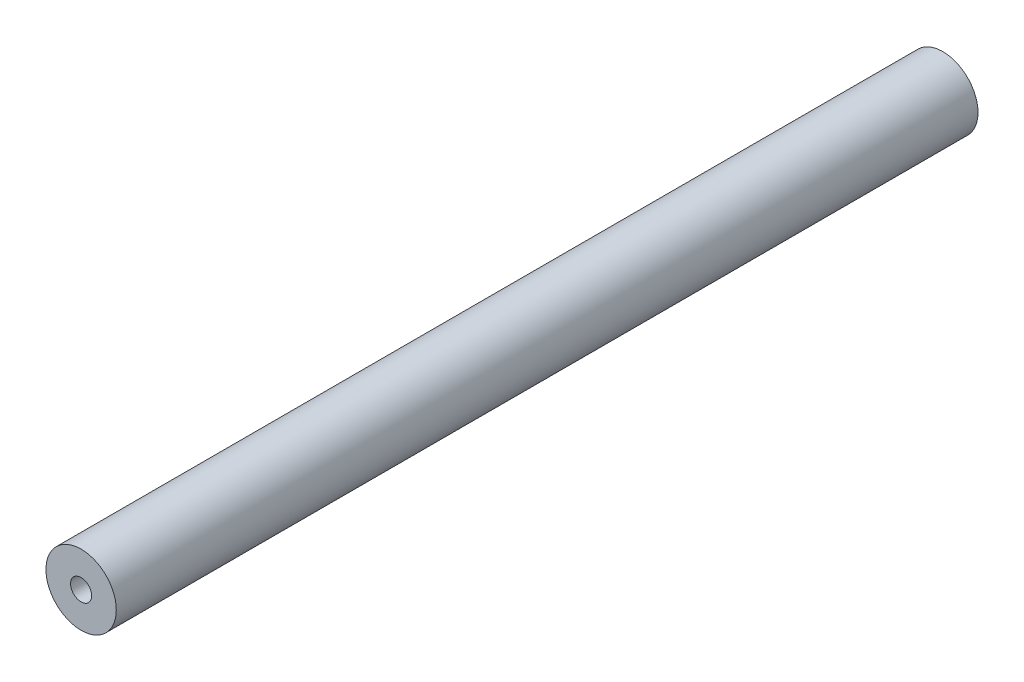
SolidWorks part; units mm, degrees
material "Cast Alloy Steel"
ref_plane "Front Plane" through (0, 0, 0) normal (0, 0, 1) x (1, 0, 0)
ref_plane "Top Plane" through (0, 0, 0) normal (0, 1, 0) x (1, 0, 0)
ref_plane "Right Plane" through (0, 0, 0) normal (1, 0, 0) x (0, 0, -1)
sketch "Sketch2" plane through (0, 0, 0) normal (0, 0, 1) x (1, 0, 0)
  circle A0 centre (0, 0) radius 100
  circle A1 centre (0, 0) radius 30
  dimension "230" = 200
  dimension "D2" = 60
extrude "Boss-Extrude1" add sketch "Sketch2" along normal blind 2450
scale "Scale1" bodies to scale 101 scale about centroid uniform scaling yes scale factor 0.1
